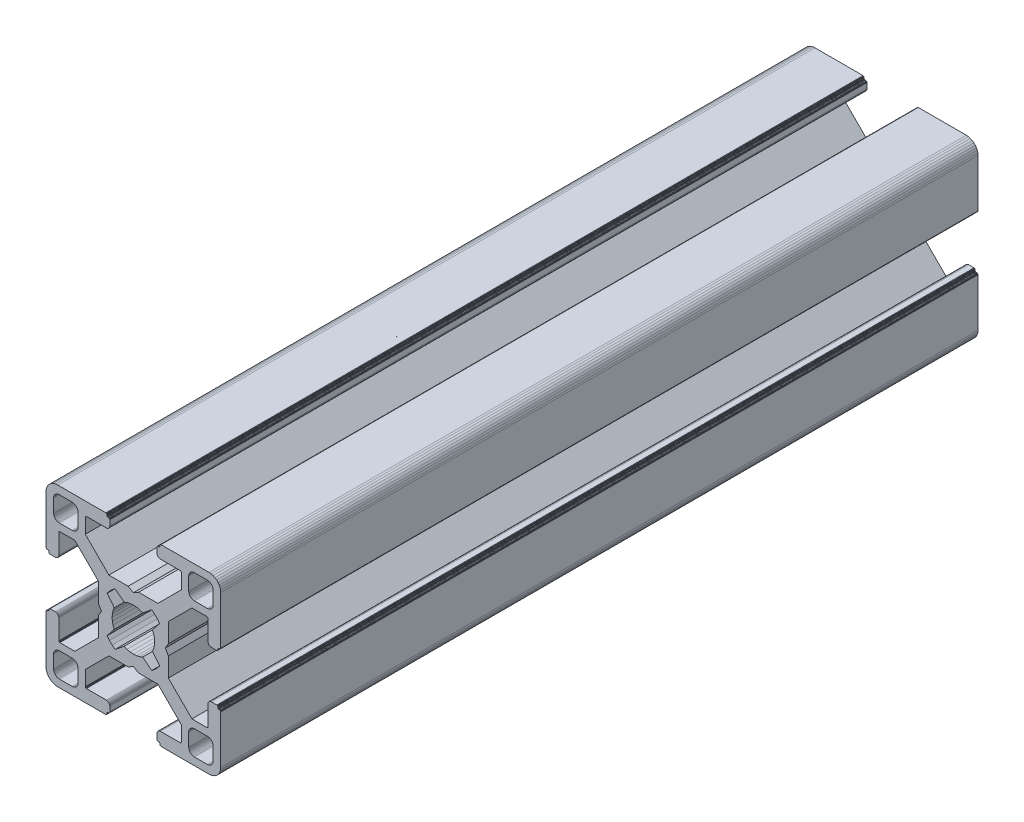
SolidWorks part; units mm, degrees
ref_plane "Front Plane" through (0, 0, 0) normal (0, 0, 1) x (1, 0, 0)
ref_plane "Top Plane" through (0, 0, 0) normal (0, 1, 0) x (1, 0, 0)
ref_plane "Right Plane" through (0, 0, 0) normal (1, 0, 0) x (0, 0, -1)
ref_plane "Plane1" through (0, 0, 0) normal (0, 0, 1) x (1, 0, 0)
sketch "Sketch1" plane through (0, 0, 0) normal (0, 0, 1) x (1, 0, 0)
  line L0 (28.3473, 29.9696) -> (28, 30)
  line L1 (28, 30) -> (19.75, 30)
  line L2 (19.75, 30) -> (19.7153, 29.997)
  line L3 (19.7153, 29.997) -> (19.6816, 29.9879)
  line L4 (19.6816, 29.9879) -> (19.65, 29.9732)
  line L5 (19.65, 29.9732) -> (19.6214, 29.9532)
  line L6 (19.6214, 29.9532) -> (19.5968, 29.9286)
  line L7 (19.5968, 29.9286) -> (19.5768, 29.9)
  line L8 (19.5768, 29.9) -> (19.5621, 29.8684)
  line L9 (19.5621, 29.8684) -> (19.553, 29.8347)
  line L10 (19.553, 29.8347) -> (19.55, 29.8)
  line L11 (19.55, 29.8) -> (19.55, 29.7)
  line L12 (19.55, 29.7) -> (19.547, 29.6653)
  line L13 (19.547, 29.6653) -> (19.5379, 29.6316)
  line L14 (19.5379, 29.6316) -> (19.5232, 29.6)
  line L15 (19.5232, 29.6) -> (19.5032, 29.5714)
  line L16 (19.5032, 29.5714) -> (19.4786, 29.5468)
  line L17 (19.4786, 29.5468) -> (19.45, 29.5268)
  line L18 (19.45, 29.5268) -> (19.4184, 29.5121)
  line L19 (19.4184, 29.5121) -> (19.3847, 29.503)
  line L20 (19.3847, 29.503) -> (19.35, 29.5)
  line L21 (19.35, 29.5) -> (19.25, 29.5)
  line L22 (19.25, 29.5) -> (19.2153, 29.497)
  line L23 (19.2153, 29.497) -> (19.1816, 29.4879)
  line L24 (19.1816, 29.4879) -> (19.15, 29.4732)
  line L25 (19.15, 29.4732) -> (19.1214, 29.4532)
  line L26 (19.1214, 29.4532) -> (19.0968, 29.4286)
  line L27 (19.0968, 29.4286) -> (19.0768, 29.4)
  line L28 (19.0768, 29.4) -> (19.0621, 29.3684)
  line L29 (19.0621, 29.3684) -> (19.053, 29.3347)
  line L30 (19.053, 29.3347) -> (19.05, 29.3)
  line L31 (19.05, 29.3) -> (19.05, 28.4)
  line L32 (19.05, 28.4) -> (19.0591, 28.2958)
  line L33 (19.0591, 28.2958) -> (19.0862, 28.1948)
  line L34 (19.0862, 28.1948) -> (19.1304, 28.1)
  line L35 (19.1304, 28.1) -> (19.1904, 28.0143)
  line L36 (19.1904, 28.0143) -> (19.2643, 27.9404)
  line L37 (19.2643, 27.9404) -> (19.35, 27.8804)
  line L38 (19.35, 27.8804) -> (19.4448, 27.8362)
  line L39 (19.4448, 27.8362) -> (19.5458, 27.8091)
  line L40 (19.5458, 27.8091) -> (19.65, 27.8)
  line L41 (19.65, 27.8) -> (23.05, 27.8)
  line L42 (23.05, 27.8) -> (23.0847, 27.7969)
  line L43 (23.0847, 27.7969) -> (23.1184, 27.7879)
  line L44 (23.1184, 27.7879) -> (23.15, 27.7732)
  line L45 (23.15, 27.7732) -> (23.1786, 27.7532)
  line L46 (23.1786, 27.7532) -> (23.2032, 27.7285)
  line L47 (23.2032, 27.7285) -> (23.2232, 27.7)
  line L48 (23.2232, 27.7) -> (23.2379, 27.6684)
  line L49 (23.2379, 27.6684) -> (23.247, 27.6347)
  line L50 (23.247, 27.6347) -> (23.25, 27.6)
  line L51 (23.25, 27.6) -> (23.25, 25.05)
  line L52 (23.25, 25.05) -> (19.2045, 21)
  line L53 (19.2045, 21) -> (15.9, 21)
  line L54 (15.9, 21) -> (15, 20.4848)
  line L55 (15, 20.4848) -> (14.1, 21)
  line L56 (14.1, 21) -> (10.7955, 21)
  line L57 (10.7955, 21) -> (7.9973, 23.8013)
  line L58 (7.9973, 23.8013) -> (6.75, 25.05)
  line L59 (6.75, 25.05) -> (6.75, 27.6)
  line L60 (6.75, 27.6) -> (6.753, 27.6347)
  line L61 (6.753, 27.6347) -> (6.7621, 27.6684)
  line L62 (6.7621, 27.6684) -> (6.7768, 27.7)
  line L63 (6.7768, 27.7) -> (6.7968, 27.7285)
  line L64 (6.7968, 27.7285) -> (6.8215, 27.7532)
  line L65 (6.8215, 27.7532) -> (6.85, 27.7732)
  line L66 (6.85, 27.7732) -> (6.8816, 27.7879)
  line L67 (6.8816, 27.7879) -> (6.9153, 27.7969)
  line L68 (6.9153, 27.7969) -> (6.95, 27.8)
  line L69 (6.95, 27.8) -> (10.35, 27.8)
  line L70 (10.35, 27.8) -> (10.4542, 27.8091)
  line L71 (10.4542, 27.8091) -> (10.5552, 27.8362)
  line L72 (10.5552, 27.8362) -> (10.65, 27.8804)
  line L73 (10.65, 27.8804) -> (10.7357, 27.9404)
  line L74 (10.7357, 27.9404) -> (10.8096, 28.0143)
  line L75 (10.8096, 28.0143) -> (10.8696, 28.1)
  line L76 (10.8696, 28.1) -> (10.9138, 28.1948)
  line L77 (10.9138, 28.1948) -> (10.9409, 28.2958)
  line L78 (10.9409, 28.2958) -> (10.95, 28.4)
  line L79 (10.95, 28.4) -> (10.95, 29.3)
  line L80 (10.95, 29.3) -> (10.947, 29.3347)
  line L81 (10.947, 29.3347) -> (10.938, 29.3684)
  line L82 (10.938, 29.3684) -> (10.9232, 29.4)
  line L83 (10.9232, 29.4) -> (10.9032, 29.4286)
  line L84 (10.9032, 29.4286) -> (10.8786, 29.4532)
  line L85 (10.8786, 29.4532) -> (10.85, 29.4732)
  line L86 (10.85, 29.4732) -> (10.8184, 29.4879)
  line L87 (10.8184, 29.4879) -> (10.7847, 29.497)
  line L88 (10.7847, 29.497) -> (10.75, 29.5)
  line L89 (10.75, 29.5) -> (10.65, 29.5)
  line L90 (10.65, 29.5) -> (10.6153, 29.503)
  line L91 (10.6153, 29.503) -> (10.5816, 29.5121)
  line L92 (10.5816, 29.5121) -> (10.55, 29.5268)
  line L93 (10.55, 29.5268) -> (10.5214, 29.5468)
  line L94 (10.5214, 29.5468) -> (10.4968, 29.5714)
  line L95 (10.4968, 29.5714) -> (10.4768, 29.6)
  line L96 (10.4768, 29.6) -> (10.4621, 29.6316)
  line L97 (10.4621, 29.6316) -> (10.453, 29.6653)
  line L98 (10.453, 29.6653) -> (10.45, 29.7)
  line L99 (10.45, 29.7) -> (10.45, 29.8)
  line L100 (10.45, 29.8) -> (10.447, 29.8347)
  line L101 (10.447, 29.8347) -> (10.4379, 29.8684)
  line L102 (10.4379, 29.8684) -> (10.4232, 29.9)
  line L103 (10.4232, 29.9) -> (10.4032, 29.9286)
  line L104 (10.4032, 29.9286) -> (10.3786, 29.9532)
  line L105 (10.3786, 29.9532) -> (10.35, 29.9732)
  line L106 (10.35, 29.9732) -> (10.3184, 29.9879)
  line L107 (10.3184, 29.9879) -> (10.2847, 29.997)
  line L108 (10.2847, 29.997) -> (10.25, 30)
  line L109 (10.25, 30) -> (2, 30)
  line L110 (2, 30) -> (1.6527, 29.9696)
  line L111 (1.6527, 29.9696) -> (1.316, 29.8794)
  line L112 (1.316, 29.8794) -> (1, 29.7321)
  line L113 (1, 29.7321) -> (0.7144, 29.5321)
  line L114 (0.7144, 29.5321) -> (0.4679, 29.2856)
  line L115 (0.4679, 29.2856) -> (0.2679, 29)
  line L116 (0.2679, 29) -> (0.1206, 28.684)
  line L117 (0.1206, 28.684) -> (0.0304, 28.3473)
  line L118 (0.0304, 28.3473) -> (0, 28)
  line L119 (0, 28) -> (0, 19.75)
  line L120 (0, 19.75) -> (0.003, 19.7153)
  line L121 (0.003, 19.7153) -> (0.0121, 19.6816)
  line L122 (0.0121, 19.6816) -> (0.0268, 19.65)
  line L123 (0.0268, 19.65) -> (0.0468, 19.6214)
  line L124 (0.0468, 19.6214) -> (0.0714, 19.5968)
  line L125 (0.0714, 19.5968) -> (0.1, 19.5768)
  line L126 (0.1, 19.5768) -> (0.1316, 19.5621)
  line L127 (0.1316, 19.5621) -> (0.1653, 19.553)
  line L128 (0.1653, 19.553) -> (0.2, 19.55)
  line L129 (0.2, 19.55) -> (0.3, 19.55)
  line L130 (0.3, 19.55) -> (0.3347, 19.547)
  line L131 (0.3347, 19.547) -> (0.3684, 19.5379)
  line L132 (0.3684, 19.5379) -> (0.4, 19.5232)
  line L133 (0.4, 19.5232) -> (0.4286, 19.5032)
  line L134 (0.4286, 19.5032) -> (0.4532, 19.4786)
  line L135 (0.4532, 19.4786) -> (0.4732, 19.45)
  line L136 (0.4732, 19.45) -> (0.4879, 19.4184)
  line L137 (0.4879, 19.4184) -> (0.497, 19.3847)
  line L138 (0.497, 19.3847) -> (0.5, 19.35)
  line L139 (0.5, 19.35) -> (0.5, 19.25)
  line L140 (0.5, 19.25) -> (0.503, 19.2153)
  line L141 (0.503, 19.2153) -> (0.5121, 19.1816)
  line L142 (0.5121, 19.1816) -> (0.5268, 19.15)
  line L143 (0.5268, 19.15) -> (0.5468, 19.1214)
  line L144 (0.5468, 19.1214) -> (0.5714, 19.0968)
  line L145 (0.5714, 19.0968) -> (0.6, 19.0768)
  line L146 (0.6, 19.0768) -> (0.6316, 19.0621)
  line L147 (0.6316, 19.0621) -> (0.6653, 19.053)
  line L148 (0.6653, 19.053) -> (0.7, 19.05)
  line L149 (0.7, 19.05) -> (1.6, 19.05)
  line L150 (1.6, 19.05) -> (1.7042, 19.0591)
  line L151 (1.7042, 19.0591) -> (1.8052, 19.0862)
  line L152 (1.8052, 19.0862) -> (1.9, 19.1304)
  line L153 (1.9, 19.1304) -> (1.9857, 19.1904)
  line L154 (1.9857, 19.1904) -> (2.0596, 19.2643)
  line L155 (2.0596, 19.2643) -> (2.1196, 19.35)
  line L156 (2.1196, 19.35) -> (2.1638, 19.4448)
  line L157 (2.1638, 19.4448) -> (2.1909, 19.5458)
  line L158 (2.1909, 19.5458) -> (2.2, 19.65)
  line L159 (2.2, 19.65) -> (2.2, 23.05)
  line L160 (2.2, 23.05) -> (2.203, 23.0847)
  line L161 (2.203, 23.0847) -> (2.2121, 23.1184)
  line L162 (2.2121, 23.1184) -> (2.2268, 23.15)
  line L163 (2.2268, 23.15) -> (2.2468, 23.1786)
  line L164 (2.2468, 23.1786) -> (2.2714, 23.2032)
  line L165 (2.2714, 23.2032) -> (2.3, 23.2232)
  line L166 (2.3, 23.2232) -> (2.3316, 23.2379)
  line L167 (2.3316, 23.2379) -> (2.3653, 23.247)
  line L168 (2.3653, 23.247) -> (2.4, 23.25)
  line L169 (2.4, 23.25) -> (4.95, 23.25)
  line L170 (4.95, 23.25) -> (7.9973, 20.2027)
  line L171 (7.9973, 20.2027) -> (8.9955, 19.2045)
  line L172 (8.9955, 19.2045) -> (8.9955, 15.9)
  line L173 (8.9955, 15.9) -> (9.5151, 15)
  line L174 (9.5151, 15) -> (8.9955, 14.1)
  line L175 (8.9955, 14.1) -> (8.9955, 10.7955)
  line L176 (8.9955, 10.7955) -> (4.95, 6.75)
  line L177 (4.95, 6.75) -> (2.4, 6.75)
  line L178 (2.4, 6.75) -> (2.3653, 6.753)
  line L179 (2.3653, 6.753) -> (2.3316, 6.7621)
  line L180 (2.3316, 6.7621) -> (2.3, 6.7768)
  line L181 (2.3, 6.7768) -> (2.2714, 6.7968)
  line L182 (2.2714, 6.7968) -> (2.2468, 6.8214)
  line L183 (2.2468, 6.8214) -> (2.2268, 6.85)
  line L184 (2.2268, 6.85) -> (2.2121, 6.8816)
  line L185 (2.2121, 6.8816) -> (2.203, 6.9153)
  line L186 (2.203, 6.9153) -> (2.2, 6.95)
  line L187 (2.2, 6.95) -> (2.2, 10.35)
  line L188 (2.2, 10.35) -> (2.1909, 10.4542)
  line L189 (2.1909, 10.4542) -> (2.1638, 10.5552)
  line L190 (2.1638, 10.5552) -> (2.1196, 10.65)
  line L191 (2.1196, 10.65) -> (2.0596, 10.7357)
  line L192 (2.0596, 10.7357) -> (1.9857, 10.8096)
  line L193 (1.9857, 10.8096) -> (1.9, 10.8696)
  line L194 (1.9, 10.8696) -> (1.8052, 10.9138)
  line L195 (1.8052, 10.9138) -> (1.7042, 10.9409)
  line L196 (1.7042, 10.9409) -> (1.6, 10.95)
  line L197 (1.6, 10.95) -> (0.7, 10.95)
  line L198 (0.7, 10.95) -> (0.6653, 10.9469)
  line L199 (0.6653, 10.9469) -> (0.6316, 10.9379)
  line L200 (0.6316, 10.9379) -> (0.6, 10.9232)
  line L201 (0.6, 10.9232) -> (0.5715, 10.9032)
  line L202 (0.5715, 10.9032) -> (0.5468, 10.8785)
  line L203 (0.5468, 10.8785) -> (0.5268, 10.85)
  line L204 (0.5268, 10.85) -> (0.5121, 10.8184)
  line L205 (0.5121, 10.8184) -> (0.503, 10.7847)
  line L206 (0.503, 10.7847) -> (0.5, 10.75)
  line L207 (0.5, 10.75) -> (0.5, 10.65)
  line L208 (0.5, 10.65) -> (0.497, 10.6153)
  line L209 (0.497, 10.6153) -> (0.4879, 10.5816)
  line L210 (0.4879, 10.5816) -> (0.4732, 10.55)
  line L211 (0.4732, 10.55) -> (0.4532, 10.5214)
  line L212 (0.4532, 10.5214) -> (0.4286, 10.4968)
  line L213 (0.4286, 10.4968) -> (0.4, 10.4768)
  line L214 (0.4, 10.4768) -> (0.3684, 10.4621)
  line L215 (0.3684, 10.4621) -> (0.3347, 10.453)
  line L216 (0.3347, 10.453) -> (0.3, 10.45)
  line L217 (0.3, 10.45) -> (0.2, 10.45)
  line L218 (0.2, 10.45) -> (0.1653, 10.447)
  line L219 (0.1653, 10.447) -> (0.1316, 10.4379)
  line L220 (0.1316, 10.4379) -> (0.1, 10.4232)
  line L221 (0.1, 10.4232) -> (0.0714, 10.4032)
  line L222 (0.0714, 10.4032) -> (0.0468, 10.3786)
  line L223 (0.0468, 10.3786) -> (0.0268, 10.35)
  line L224 (0.0268, 10.35) -> (0.0121, 10.3184)
  line L225 (0.0121, 10.3184) -> (0.003, 10.2847)
  line L226 (0.003, 10.2847) -> (0, 10.25)
  line L227 (0, 10.25) -> (0, 2)
  line L228 (0, 2) -> (0.0304, 1.6527)
  line L229 (0.0304, 1.6527) -> (0.1206, 1.316)
  line L230 (0.1206, 1.316) -> (0.2679, 1)
  line L231 (0.2679, 1) -> (0.4679, 0.7144)
  line L232 (0.4679, 0.7144) -> (0.7144, 0.4679)
  line L233 (0.7144, 0.4679) -> (1, 0.2679)
  line L234 (1, 0.2679) -> (1.316, 0.1206)
  line L235 (1.316, 0.1206) -> (1.6527, 0.0304)
  line L236 (1.6527, 0.0304) -> (2, 0)
  line L237 (2, 0) -> (10.25, 0)
  line L238 (10.25, 0) -> (10.2847, 0.003)
  line L239 (10.2847, 0.003) -> (10.3184, 0.0121)
  line L240 (10.3184, 0.0121) -> (10.35, 0.0268)
  line L241 (10.35, 0.0268) -> (10.3786, 0.0468)
  line L242 (10.3786, 0.0468) -> (10.4032, 0.0714)
  line L243 (10.4032, 0.0714) -> (10.4232, 0.1)
  line L244 (10.4232, 0.1) -> (10.4379, 0.1316)
  line L245 (10.4379, 0.1316) -> (10.447, 0.1653)
  line L246 (10.447, 0.1653) -> (10.45, 0.2)
  line L247 (10.45, 0.2) -> (10.45, 0.3)
  line L248 (10.45, 0.3) -> (10.453, 0.3347)
  line L249 (10.453, 0.3347) -> (10.4621, 0.3684)
  line L250 (10.4621, 0.3684) -> (10.4768, 0.4)
  line L251 (10.4768, 0.4) -> (10.4968, 0.4286)
  line L252 (10.4968, 0.4286) -> (10.5214, 0.4532)
  line L253 (10.5214, 0.4532) -> (10.55, 0.4732)
  line L254 (10.55, 0.4732) -> (10.5816, 0.4879)
  line L255 (10.5816, 0.4879) -> (10.6153, 0.497)
  line L256 (10.6153, 0.497) -> (10.65, 0.5)
  line L257 (10.65, 0.5) -> (10.75, 0.5)
  line L258 (10.75, 0.5) -> (10.7847, 0.503)
  line L259 (10.7847, 0.503) -> (10.8184, 0.5121)
  line L260 (10.8184, 0.5121) -> (10.85, 0.5268)
  line L261 (10.85, 0.5268) -> (10.8785, 0.5468)
  line L262 (10.8785, 0.5468) -> (10.9032, 0.5715)
  line L263 (10.9032, 0.5715) -> (10.9232, 0.6)
  line L264 (10.9232, 0.6) -> (10.9379, 0.6316)
  line L265 (10.9379, 0.6316) -> (10.9469, 0.6653)
  line L266 (10.9469, 0.6653) -> (10.95, 0.7)
  line L267 (10.95, 0.7) -> (10.95, 1.6)
  line L268 (10.95, 1.6) -> (10.9409, 1.7042)
  line L269 (10.9409, 1.7042) -> (10.9138, 1.8052)
  line L270 (10.9138, 1.8052) -> (10.8696, 1.9)
  line L271 (10.8696, 1.9) -> (10.8096, 1.9857)
  line L272 (10.8096, 1.9857) -> (10.7357, 2.0596)
  line L273 (10.7357, 2.0596) -> (10.65, 2.1196)
  line L274 (10.65, 2.1196) -> (10.5552, 2.1638)
  line L275 (10.5552, 2.1638) -> (10.4542, 2.1909)
  line L276 (10.4542, 2.1909) -> (10.35, 2.2)
  line L277 (10.35, 2.2) -> (6.95, 2.2)
  line L278 (6.95, 2.2) -> (6.9153, 2.203)
  line L279 (6.9153, 2.203) -> (6.8816, 2.212)
  line L280 (6.8816, 2.212) -> (6.85, 2.2268)
  line L281 (6.85, 2.2268) -> (6.8215, 2.2468)
  line L282 (6.8215, 2.2468) -> (6.7968, 2.2714)
  line L283 (6.7968, 2.2714) -> (6.7768, 2.3)
  line L284 (6.7768, 2.3) -> (6.7621, 2.3316)
  line L285 (6.7621, 2.3316) -> (6.753, 2.3653)
  line L286 (6.753, 2.3653) -> (6.75, 2.4)
  line L287 (6.75, 2.4) -> (6.75, 4.95)
  line L288 (6.75, 4.95) -> (9.7875, 7.9908)
  line L289 (9.7875, 7.9908) -> (10.7955, 9)
  line L290 (10.7955, 9) -> (14.1, 9)
  line L291 (14.1, 9) -> (15, 9.5151)
  line L292 (15, 9.5151) -> (15.9, 9)
  line L293 (15.9, 9) -> (19.2045, 9)
  line L294 (19.2045, 9) -> (20.2126, 7.9908)
  line L295 (20.2126, 7.9908) -> (23.25, 4.95)
  line L296 (23.25, 4.95) -> (23.25, 2.4)
  line L297 (23.25, 2.4) -> (23.247, 2.3653)
  line L298 (23.247, 2.3653) -> (23.2379, 2.3316)
  line L299 (23.2379, 2.3316) -> (23.2232, 2.3)
  line L300 (23.2232, 2.3) -> (23.2032, 2.2714)
  line L301 (23.2032, 2.2714) -> (23.1786, 2.2468)
  line L302 (23.1786, 2.2468) -> (23.15, 2.2268)
  line L303 (23.15, 2.2268) -> (23.1184, 2.212)
  line L304 (23.1184, 2.212) -> (23.0847, 2.203)
  line L305 (23.0847, 2.203) -> (23.05, 2.2)
  line L306 (23.05, 2.2) -> (19.65, 2.2)
  line L307 (19.65, 2.2) -> (19.5458, 2.1909)
  line L308 (19.5458, 2.1909) -> (19.4448, 2.1638)
  line L309 (19.4448, 2.1638) -> (19.35, 2.1196)
  line L310 (19.35, 2.1196) -> (19.2643, 2.0596)
  line L311 (19.2643, 2.0596) -> (19.1904, 1.9857)
  line L312 (19.1904, 1.9857) -> (19.1304, 1.9)
  line L313 (19.1304, 1.9) -> (19.0862, 1.8052)
  line L314 (19.0862, 1.8052) -> (19.0591, 1.7042)
  line L315 (19.0591, 1.7042) -> (19.05, 1.6)
  line L316 (19.05, 1.6) -> (19.05, 0.7)
  line L317 (19.05, 0.7) -> (19.053, 0.6653)
  line L318 (19.053, 0.6653) -> (19.0621, 0.6316)
  line L319 (19.0621, 0.6316) -> (19.0768, 0.6)
  line L320 (19.0768, 0.6) -> (19.0968, 0.5714)
  line L321 (19.0968, 0.5714) -> (19.1214, 0.5468)
  line L322 (19.1214, 0.5468) -> (19.15, 0.5268)
  line L323 (19.15, 0.5268) -> (19.1816, 0.5121)
  line L324 (19.1816, 0.5121) -> (19.2153, 0.503)
  line L325 (19.2153, 0.503) -> (19.25, 0.5)
  line L326 (19.25, 0.5) -> (19.35, 0.5)
  line L327 (19.35, 0.5) -> (19.3847, 0.497)
  line L328 (19.3847, 0.497) -> (19.4184, 0.4879)
  line L329 (19.4184, 0.4879) -> (19.45, 0.4732)
  line L330 (19.45, 0.4732) -> (19.4786, 0.4532)
  line L331 (19.4786, 0.4532) -> (19.5032, 0.4286)
  line L332 (19.5032, 0.4286) -> (19.5232, 0.4)
  line L333 (19.5232, 0.4) -> (19.5379, 0.3684)
  line L334 (19.5379, 0.3684) -> (19.547, 0.3347)
  line L335 (19.547, 0.3347) -> (19.55, 0.3)
  line L336 (19.55, 0.3) -> (19.55, 0.2)
  line L337 (19.55, 0.2) -> (19.553, 0.1653)
  line L338 (19.553, 0.1653) -> (19.5621, 0.1316)
  line L339 (19.5621, 0.1316) -> (19.5768, 0.1)
  line L340 (19.5768, 0.1) -> (19.5968, 0.0714)
  line L341 (19.5968, 0.0714) -> (19.6214, 0.0468)
  line L342 (19.6214, 0.0468) -> (19.65, 0.0268)
  line L343 (19.65, 0.0268) -> (19.6816, 0.0121)
  line L344 (19.6816, 0.0121) -> (19.7153, 0.003)
  line L345 (19.7153, 0.003) -> (19.75, 0)
  line L346 (19.75, 0) -> (28, 0)
  line L347 (28, 0) -> (28.3473, 0.0304)
  line L348 (28.3473, 0.0304) -> (28.684, 0.1206)
  line L349 (28.684, 0.1206) -> (29, 0.2679)
  line L350 (29, 0.2679) -> (29.2856, 0.4679)
  line L351 (29.2856, 0.4679) -> (29.5321, 0.7144)
  line L352 (29.5321, 0.7144) -> (29.7321, 1)
  line L353 (29.7321, 1) -> (29.8794, 1.316)
  line L354 (29.8794, 1.316) -> (29.9696, 1.6527)
  line L355 (29.9696, 1.6527) -> (30, 2)
  line L356 (30, 2) -> (30, 10.25)
  line L357 (30, 10.25) -> (29.997, 10.2847)
  line L358 (29.997, 10.2847) -> (29.988, 10.3184)
  line L359 (29.988, 10.3184) -> (29.9732, 10.35)
  line L360 (29.9732, 10.35) -> (29.9532, 10.3785)
  line L361 (29.9532, 10.3785) -> (29.9286, 10.4032)
  line L362 (29.9286, 10.4032) -> (29.9, 10.4232)
  line L363 (29.9, 10.4232) -> (29.8684, 10.4379)
  line L364 (29.8684, 10.4379) -> (29.8347, 10.447)
  line L365 (29.8347, 10.447) -> (29.8, 10.45)
  line L366 (29.8, 10.45) -> (29.7, 10.45)
  line L367 (29.7, 10.45) -> (29.6649, 10.4534)
  line L368 (29.6649, 10.4534) -> (29.6312, 10.4624)
  line L369 (29.6312, 10.4624) -> (29.5996, 10.4772)
  line L370 (29.5996, 10.4772) -> (29.5711, 10.4972)
  line L371 (29.5711, 10.4972) -> (29.5464, 10.5218)
  line L372 (29.5464, 10.5218) -> (29.5264, 10.5504)
  line L373 (29.5264, 10.5504) -> (29.5117, 10.582)
  line L374 (29.5117, 10.582) -> (29.5027, 10.6156)
  line L375 (29.5027, 10.6156) -> (29.4996, 10.6504)
  line L376 (29.4996, 10.6504) -> (29.4996, 10.7504)
  line L377 (29.4996, 10.7504) -> (29.497, 10.7847)
  line L378 (29.497, 10.7847) -> (29.4879, 10.8184)
  line L379 (29.4879, 10.8184) -> (29.4732, 10.85)
  line L380 (29.4732, 10.85) -> (29.4532, 10.8785)
  line L381 (29.4532, 10.8785) -> (29.4286, 10.9032)
  line L382 (29.4286, 10.9032) -> (29.4, 10.9232)
  line L383 (29.4, 10.9232) -> (29.3684, 10.9379)
  line L384 (29.3684, 10.9379) -> (29.3347, 10.9469)
  line L385 (29.3347, 10.9469) -> (29.3, 10.95)
  line L386 (29.3, 10.95) -> (28.4, 10.95)
  line L387 (28.4, 10.95) -> (28.2958, 10.9409)
  line L388 (28.2958, 10.9409) -> (28.1948, 10.9138)
  line L389 (28.1948, 10.9138) -> (28.1, 10.8696)
  line L390 (28.1, 10.8696) -> (28.0143, 10.8096)
  line L391 (28.0143, 10.8096) -> (27.9404, 10.7357)
  line L392 (27.9404, 10.7357) -> (27.8804, 10.65)
  line L393 (27.8804, 10.65) -> (27.8362, 10.5552)
  line L394 (27.8362, 10.5552) -> (27.8091, 10.4542)
  line L395 (27.8091, 10.4542) -> (27.8, 10.35)
  line L396 (27.8, 10.35) -> (27.8, 6.95)
  line L397 (27.8, 6.95) -> (27.797, 6.9153)
  line L398 (27.797, 6.9153) -> (27.7879, 6.8816)
  line L399 (27.7879, 6.8816) -> (27.7732, 6.85)
  line L400 (27.7732, 6.85) -> (27.7532, 6.8214)
  line L401 (27.7532, 6.8214) -> (27.7286, 6.7968)
  line L402 (27.7286, 6.7968) -> (27.7, 6.7768)
  line L403 (27.7, 6.7768) -> (27.6684, 6.7621)
  line L404 (27.6684, 6.7621) -> (27.6347, 6.753)
  line L405 (27.6347, 6.753) -> (27.6, 6.75)
  line L406 (27.6, 6.75) -> (25.05, 6.75)
  line L407 (25.05, 6.75) -> (23.8092, 7.9908)
  line L408 (23.8092, 7.9908) -> (21.0045, 10.7955)
  line L409 (21.0045, 10.7955) -> (21.0045, 14.1)
  line L410 (21.0045, 14.1) -> (20.4849, 15)
  line L411 (20.4849, 15) -> (21.0045, 15.9)
  line L412 (21.0045, 15.9) -> (21.0045, 19.2045)
  line L413 (21.0045, 19.2045) -> (25.05, 23.25)
  line L414 (25.05, 23.25) -> (27.6, 23.25)
  line L415 (27.6, 23.25) -> (27.6347, 23.247)
  line L416 (27.6347, 23.247) -> (27.6684, 23.2379)
  line L417 (27.6684, 23.2379) -> (27.7, 23.2232)
  line L418 (27.7, 23.2232) -> (27.7286, 23.2032)
  line L419 (27.7286, 23.2032) -> (27.7532, 23.1786)
  line L420 (27.7532, 23.1786) -> (27.7732, 23.15)
  line L421 (27.7732, 23.15) -> (27.7879, 23.1184)
  line L422 (27.7879, 23.1184) -> (27.797, 23.0847)
  line L423 (27.797, 23.0847) -> (27.8, 23.05)
  line L424 (27.8, 23.05) -> (27.8, 19.65)
  line L425 (27.8, 19.65) -> (27.8091, 19.5458)
  line L426 (27.8091, 19.5458) -> (27.8362, 19.4448)
  line L427 (27.8362, 19.4448) -> (27.8804, 19.35)
  line L428 (27.8804, 19.35) -> (27.9404, 19.2643)
  line L429 (27.9404, 19.2643) -> (28.0143, 19.1904)
  line L430 (28.0143, 19.1904) -> (28.1, 19.1304)
  line L431 (28.1, 19.1304) -> (28.1948, 19.0862)
  line L432 (28.1948, 19.0862) -> (28.2958, 19.0591)
  line L433 (28.2958, 19.0591) -> (28.4, 19.05)
  line L434 (28.4, 19.05) -> (29.3, 19.05)
  line L435 (29.3, 19.05) -> (29.3347, 19.053)
  line L436 (29.3347, 19.053) -> (29.3684, 19.0621)
  line L437 (29.3684, 19.0621) -> (29.4, 19.0768)
  line L438 (29.4, 19.0768) -> (29.4282, 19.0971)
  line L439 (29.4282, 19.0971) -> (29.4528, 19.1218)
  line L440 (29.4528, 19.1218) -> (29.4728, 19.1504)
  line L441 (29.4728, 19.1504) -> (29.4876, 19.182)
  line L442 (29.4876, 19.182) -> (29.4966, 19.2156)
  line L443 (29.4966, 19.2156) -> (29.4996, 19.2504)
  line L444 (29.4996, 19.2504) -> (29.4996, 19.3504)
  line L445 (29.4996, 19.3504) -> (29.5027, 19.3851)
  line L446 (29.5027, 19.3851) -> (29.5117, 19.4188)
  line L447 (29.5117, 19.4188) -> (29.5264, 19.4504)
  line L448 (29.5264, 19.4504) -> (29.5464, 19.4789)
  line L449 (29.5464, 19.4789) -> (29.5711, 19.5036)
  line L450 (29.5711, 19.5036) -> (29.5996, 19.5236)
  line L451 (29.5996, 19.5236) -> (29.6312, 19.5383)
  line L452 (29.6312, 19.5383) -> (29.6649, 19.5473)
  line L453 (29.6649, 19.5473) -> (29.7, 19.55)
  line L454 (29.7, 19.55) -> (29.8, 19.55)
  line L455 (29.8, 19.55) -> (29.8347, 19.553)
  line L456 (29.8347, 19.553) -> (29.8684, 19.5621)
  line L457 (29.8684, 19.5621) -> (29.9, 19.5768)
  line L458 (29.9, 19.5768) -> (29.9286, 19.5968)
  line L459 (29.9286, 19.5968) -> (29.9532, 19.6214)
  line L460 (29.9532, 19.6214) -> (29.9732, 19.65)
  line L461 (29.9732, 19.65) -> (29.9879, 19.6816)
  line L462 (29.9879, 19.6816) -> (29.997, 19.7153)
  line L463 (29.997, 19.7153) -> (30, 19.75)
  line L464 (30, 19.75) -> (30, 28)
  line L465 (30, 28) -> (29.9696, 28.3473)
  line L466 (29.9696, 28.3473) -> (29.8794, 28.684)
  line L467 (29.8794, 28.684) -> (29.7321, 29)
  line L468 (29.7321, 29) -> (29.5321, 29.2856)
  line L469 (29.5321, 29.2856) -> (29.2856, 29.5321)
  line L470 (29.2856, 29.5321) -> (29, 29.7321)
  line L471 (29, 29.7321) -> (28.684, 29.8794)
  line L472 (28.684, 29.8794) -> (28.3473, 29.9696)
  line L473 (1.3, 25.5) -> (1.3, 27.7)
  line L474 (1.3, 27.7) -> (1.3123, 27.8564)
  line L475 (1.3123, 27.8564) -> (1.3489, 28.009)
  line L476 (1.3489, 28.009) -> (1.409, 28.154)
  line L477 (1.409, 28.154) -> (1.491, 28.2878)
  line L478 (1.491, 28.2878) -> (1.5929, 28.4071)
  line L479 (1.5929, 28.4071) -> (1.7122, 28.509)
  line L480 (1.7122, 28.509) -> (1.846, 28.591)
  line L481 (1.846, 28.591) -> (1.991, 28.6511)
  line L482 (1.991, 28.6511) -> (2.1436, 28.6877)
  line L483 (2.1436, 28.6877) -> (2.3, 28.7)
  line L484 (2.3, 28.7) -> (4.5, 28.7)
  line L485 (4.5, 28.7) -> (4.6564, 28.6877)
  line L486 (4.6564, 28.6877) -> (4.809, 28.6511)
  line L487 (4.809, 28.6511) -> (4.954, 28.591)
  line L488 (4.954, 28.591) -> (5.0878, 28.509)
  line L489 (5.0878, 28.509) -> (5.2071, 28.4071)
  line L490 (5.2071, 28.4071) -> (5.309, 28.2878)
  line L491 (5.309, 28.2878) -> (5.391, 28.154)
  line L492 (5.391, 28.154) -> (5.4511, 28.009)
  line L493 (5.4511, 28.009) -> (5.4877, 27.8564)
  line L494 (5.4877, 27.8564) -> (5.5, 27.7)
  line L495 (5.5, 27.7) -> (5.5, 25.5)
  line L496 (5.5, 25.5) -> (5.4877, 25.3436)
  line L497 (5.4877, 25.3436) -> (5.4511, 25.191)
  line L498 (5.4511, 25.191) -> (5.391, 25.046)
  line L499 (5.391, 25.046) -> (5.309, 24.9122)
  line L500 (5.309, 24.9122) -> (5.2071, 24.7929)
  line L501 (5.2071, 24.7929) -> (5.0878, 24.691)
  line L502 (5.0878, 24.691) -> (4.954, 24.609)
  line L503 (4.954, 24.609) -> (4.809, 24.5489)
  line L504 (4.809, 24.5489) -> (4.6564, 24.5123)
  line L505 (4.6564, 24.5123) -> (4.5, 24.5)
  line L506 (4.5, 24.5) -> (2.3, 24.5)
  line L507 (2.3, 24.5) -> (2.1436, 24.5123)
  line L508 (2.1436, 24.5123) -> (1.991, 24.5489)
  line L509 (1.991, 24.5489) -> (1.846, 24.609)
  line L510 (1.846, 24.609) -> (1.7122, 24.691)
  line L511 (1.7122, 24.691) -> (1.5929, 24.7929)
  line L512 (1.5929, 24.7929) -> (1.491, 24.9122)
  line L513 (1.491, 24.9122) -> (1.409, 25.046)
  line L514 (1.409, 25.046) -> (1.3489, 25.191)
  line L515 (1.3489, 25.191) -> (1.3123, 25.3436)
  line L516 (1.3123, 25.3436) -> (1.3, 25.5)
  line L517 (25.3436, 28.6877) -> (25.5, 28.7)
  line L518 (25.5, 28.7) -> (27.7, 28.7)
  line L519 (27.7, 28.7) -> (27.8564, 28.6877)
  line L520 (27.8564, 28.6877) -> (28.009, 28.6511)
  line L521 (28.009, 28.6511) -> (28.154, 28.591)
  line L522 (28.154, 28.591) -> (28.2878, 28.509)
  line L523 (28.2878, 28.509) -> (28.4071, 28.4071)
  line L524 (28.4071, 28.4071) -> (28.509, 28.2878)
  line L525 (28.509, 28.2878) -> (28.591, 28.154)
  line L526 (28.591, 28.154) -> (28.6511, 28.009)
  line L527 (28.6511, 28.009) -> (28.6877, 27.8564)
  line L528 (28.6877, 27.8564) -> (28.7, 27.7)
  line L529 (28.7, 27.7) -> (28.7, 25.5)
  line L530 (28.7, 25.5) -> (28.6877, 25.3436)
  line L531 (28.6877, 25.3436) -> (28.6511, 25.191)
  line L532 (28.6511, 25.191) -> (28.591, 25.046)
  line L533 (28.591, 25.046) -> (28.509, 24.9122)
  line L534 (28.509, 24.9122) -> (28.4071, 24.7929)
  line L535 (28.4071, 24.7929) -> (28.2878, 24.691)
  line L536 (28.2878, 24.691) -> (28.154, 24.609)
  line L537 (28.154, 24.609) -> (28.009, 24.5489)
  line L538 (28.009, 24.5489) -> (27.8564, 24.5123)
  line L539 (27.8564, 24.5123) -> (27.7, 24.5)
  line L540 (27.7, 24.5) -> (25.5, 24.5)
  line L541 (25.5, 24.5) -> (25.3436, 24.5123)
  line L542 (25.3436, 24.5123) -> (25.191, 24.5489)
  line L543 (25.191, 24.5489) -> (25.046, 24.609)
  line L544 (25.046, 24.609) -> (24.9122, 24.691)
  line L545 (24.9122, 24.691) -> (24.7929, 24.7929)
  line L546 (24.7929, 24.7929) -> (24.691, 24.9122)
  line L547 (24.691, 24.9122) -> (24.609, 25.046)
  line L548 (24.609, 25.046) -> (24.5489, 25.191)
  line L549 (24.5489, 25.191) -> (24.5123, 25.3436)
  line L550 (24.5123, 25.3436) -> (24.5, 25.5)
  line L551 (24.5, 25.5) -> (24.5, 27.7)
  line L552 (24.5, 27.7) -> (24.5123, 27.8564)
  line L553 (24.5123, 27.8564) -> (24.5489, 28.009)
  line L554 (24.5489, 28.009) -> (24.609, 28.154)
  line L555 (24.609, 28.154) -> (24.691, 28.2878)
  line L556 (24.691, 28.2878) -> (24.7929, 28.4071)
  line L557 (24.7929, 28.4071) -> (24.9122, 28.509)
  line L558 (24.9122, 28.509) -> (25.046, 28.591)
  line L559 (25.046, 28.591) -> (25.191, 28.6511)
  line L560 (25.191, 28.6511) -> (25.3436, 28.6877)
  line L561 (15, 18.65) -> (15.55, 18.6083)
  line L562 (15.55, 18.6083) -> (16.0875, 18.4842)
  line L563 (16.0875, 18.4842) -> (16.6001, 18.2806)
  line L564 (16.6001, 18.2806) -> (18.1359, 19.5184)
  line L565 (18.1359, 19.5184) -> (18.645, 19.1187)
  line L566 (18.645, 19.1187) -> (19.1036, 18.6621)
  line L567 (19.1036, 18.6621) -> (19.5053, 18.1547)
  line L568 (19.5053, 18.1547) -> (18.2806, 16.6001)
  line L569 (18.2806, 16.6001) -> (18.4842, 16.0875)
  line L570 (18.4842, 16.0875) -> (18.6083, 15.55)
  line L571 (18.6083, 15.55) -> (18.65, 15)
  line L572 (18.65, 15) -> (18.6083, 14.45)
  line L573 (18.6083, 14.45) -> (18.4842, 13.9125)
  line L574 (18.4842, 13.9125) -> (18.2806, 13.3999)
  line L575 (18.2806, 13.3999) -> (19.5053, 11.8453)
  line L576 (19.5053, 11.8453) -> (19.1036, 11.3379)
  line L577 (19.1036, 11.3379) -> (18.645, 10.8813)
  line L578 (18.645, 10.8813) -> (18.1359, 10.4816)
  line L579 (18.1359, 10.4816) -> (16.6001, 11.7194)
  line L580 (16.6001, 11.7194) -> (16.0875, 11.5158)
  line L581 (16.0875, 11.5158) -> (15.55, 11.3917)
  line L582 (15.55, 11.3917) -> (15, 11.35)
  line L583 (15, 11.35) -> (14.45, 11.3917)
  line L584 (14.45, 11.3917) -> (13.9125, 11.5158)
  line L585 (13.9125, 11.5158) -> (13.3999, 11.7194)
  line L586 (13.3999, 11.7194) -> (11.8641, 10.4816)
  line L587 (11.8641, 10.4816) -> (11.355, 10.8813)
  line L588 (11.355, 10.8813) -> (10.8964, 11.3379)
  line L589 (10.8964, 11.3379) -> (10.4947, 11.8453)
  line L590 (10.4947, 11.8453) -> (11.7194, 13.3999)
  line L591 (11.7194, 13.3999) -> (11.5158, 13.9125)
  line L592 (11.5158, 13.9125) -> (11.3917, 14.45)
  line L593 (11.3917, 14.45) -> (11.35, 15)
  line L594 (11.35, 15) -> (11.3917, 15.55)
  line L595 (11.3917, 15.55) -> (11.5158, 16.0875)
  line L596 (11.5158, 16.0875) -> (11.7194, 16.6001)
  line L597 (11.7194, 16.6001) -> (10.4947, 18.1547)
  line L598 (10.4947, 18.1547) -> (10.8964, 18.6621)
  line L599 (10.8964, 18.6621) -> (11.355, 19.1187)
  line L600 (11.355, 19.1187) -> (11.8641, 19.5184)
  line L601 (11.8641, 19.5184) -> (13.3999, 18.2806)
  line L602 (13.3999, 18.2806) -> (13.9125, 18.4842)
  line L603 (13.9125, 18.4842) -> (14.45, 18.6083)
  line L604 (14.45, 18.6083) -> (15, 18.65)
  line L605 (4.5, 1.3) -> (2.3, 1.3)
  line L606 (2.3, 1.3) -> (2.1436, 1.3123)
  line L607 (2.1436, 1.3123) -> (1.991, 1.3489)
  line L608 (1.991, 1.3489) -> (1.846, 1.409)
  line L609 (1.846, 1.409) -> (1.7122, 1.491)
  line L610 (1.7122, 1.491) -> (1.5929, 1.5929)
  line L611 (1.5929, 1.5929) -> (1.491, 1.7122)
  line L612 (1.491, 1.7122) -> (1.409, 1.846)
  line L613 (1.409, 1.846) -> (1.3489, 1.991)
  line L614 (1.3489, 1.991) -> (1.3123, 2.1436)
  line L615 (1.3123, 2.1436) -> (1.3, 2.3)
  line L616 (1.3, 2.3) -> (1.3, 4.5)
  line L617 (1.3, 4.5) -> (1.3123, 4.6564)
  line L618 (1.3123, 4.6564) -> (1.3489, 4.809)
  line L619 (1.3489, 4.809) -> (1.409, 4.954)
  line L620 (1.409, 4.954) -> (1.491, 5.0878)
  line L621 (1.491, 5.0878) -> (1.5929, 5.2071)
  line L622 (1.5929, 5.2071) -> (1.7122, 5.309)
  line L623 (1.7122, 5.309) -> (1.846, 5.391)
  line L624 (1.846, 5.391) -> (1.991, 5.4511)
  line L625 (1.991, 5.4511) -> (2.1436, 5.4877)
  line L626 (2.1436, 5.4877) -> (2.3, 5.5)
  line L627 (2.3, 5.5) -> (4.5, 5.5)
  line L628 (4.5, 5.5) -> (4.6564, 5.4877)
  line L629 (4.6564, 5.4877) -> (4.809, 5.4511)
  line L630 (4.809, 5.4511) -> (4.954, 5.391)
  line L631 (4.954, 5.391) -> (5.0878, 5.309)
  line L632 (5.0878, 5.309) -> (5.2071, 5.2071)
  line L633 (5.2071, 5.2071) -> (5.309, 5.0878)
  line L634 (5.309, 5.0878) -> (5.391, 4.954)
  line L635 (5.391, 4.954) -> (5.4511, 4.809)
  line L636 (5.4511, 4.809) -> (5.4877, 4.6564)
  line L637 (5.4877, 4.6564) -> (5.5, 4.5)
  line L638 (5.5, 4.5) -> (5.5, 2.3)
  line L639 (5.5, 2.3) -> (5.4877, 2.1436)
  line L640 (5.4877, 2.1436) -> (5.4511, 1.991)
  line L641 (5.4511, 1.991) -> (5.391, 1.846)
  line L642 (5.391, 1.846) -> (5.309, 1.7122)
  line L643 (5.309, 1.7122) -> (5.2071, 1.5929)
  line L644 (5.2071, 1.5929) -> (5.0878, 1.491)
  line L645 (5.0878, 1.491) -> (4.954, 1.409)
  line L646 (4.954, 1.409) -> (4.809, 1.3489)
  line L647 (4.809, 1.3489) -> (4.6564, 1.3123)
  line L648 (4.6564, 1.3123) -> (4.5, 1.3)
  line L649 (27.7, 1.3) -> (25.5, 1.3)
  line L650 (25.5, 1.3) -> (25.3436, 1.3123)
  line L651 (25.3436, 1.3123) -> (25.191, 1.3489)
  line L652 (25.191, 1.3489) -> (25.046, 1.409)
  line L653 (25.046, 1.409) -> (24.9122, 1.491)
  line L654 (24.9122, 1.491) -> (24.7929, 1.5929)
  line L655 (24.7929, 1.5929) -> (24.691, 1.7122)
  line L656 (24.691, 1.7122) -> (24.609, 1.846)
  line L657 (24.609, 1.846) -> (24.5489, 1.991)
  line L658 (24.5489, 1.991) -> (24.5123, 2.1436)
  line L659 (24.5123, 2.1436) -> (24.5, 2.3)
  line L660 (24.5, 2.3) -> (24.5, 4.5)
  line L661 (24.5, 4.5) -> (24.5123, 4.6564)
  line L662 (24.5123, 4.6564) -> (24.5489, 4.809)
  line L663 (24.5489, 4.809) -> (24.609, 4.954)
  line L664 (24.609, 4.954) -> (24.691, 5.0878)
  line L665 (24.691, 5.0878) -> (24.7929, 5.2071)
  line L666 (24.7929, 5.2071) -> (24.9122, 5.309)
  line L667 (24.9122, 5.309) -> (25.046, 5.391)
  line L668 (25.046, 5.391) -> (25.191, 5.4511)
  line L669 (25.191, 5.4511) -> (25.3436, 5.4877)
  line L670 (25.3436, 5.4877) -> (25.5, 5.5)
  line L671 (25.5, 5.5) -> (27.7, 5.5)
  line L672 (27.7, 5.5) -> (27.8564, 5.4877)
  line L673 (27.8564, 5.4877) -> (28.009, 5.4511)
  line L674 (28.009, 5.4511) -> (28.154, 5.391)
  line L675 (28.154, 5.391) -> (28.2878, 5.309)
  line L676 (28.2878, 5.309) -> (28.4071, 5.2071)
  line L677 (28.4071, 5.2071) -> (28.509, 5.0878)
  line L678 (28.509, 5.0878) -> (28.591, 4.954)
  line L679 (28.591, 4.954) -> (28.6511, 4.809)
  line L680 (28.6511, 4.809) -> (28.6877, 4.6564)
  line L681 (28.6877, 4.6564) -> (28.7, 4.5)
  line L682 (28.7, 4.5) -> (28.7, 2.3)
  line L683 (28.7, 2.3) -> (28.6877, 2.1436)
  line L684 (28.6877, 2.1436) -> (28.6511, 1.991)
  line L685 (28.6511, 1.991) -> (28.591, 1.846)
  line L686 (28.591, 1.846) -> (28.509, 1.7122)
  line L687 (28.509, 1.7122) -> (28.4071, 1.5929)
  line L688 (28.4071, 1.5929) -> (28.2878, 1.491)
  line L689 (28.2878, 1.491) -> (28.154, 1.409)
  line L690 (28.154, 1.409) -> (28.009, 1.3489)
  line L691 (28.009, 1.3489) -> (27.8564, 1.3123)
  line L692 (27.8564, 1.3123) -> (27.7, 1.3)
extrude "Boss-Extrude1" add sketch "Sketch1" against normal blind 130
